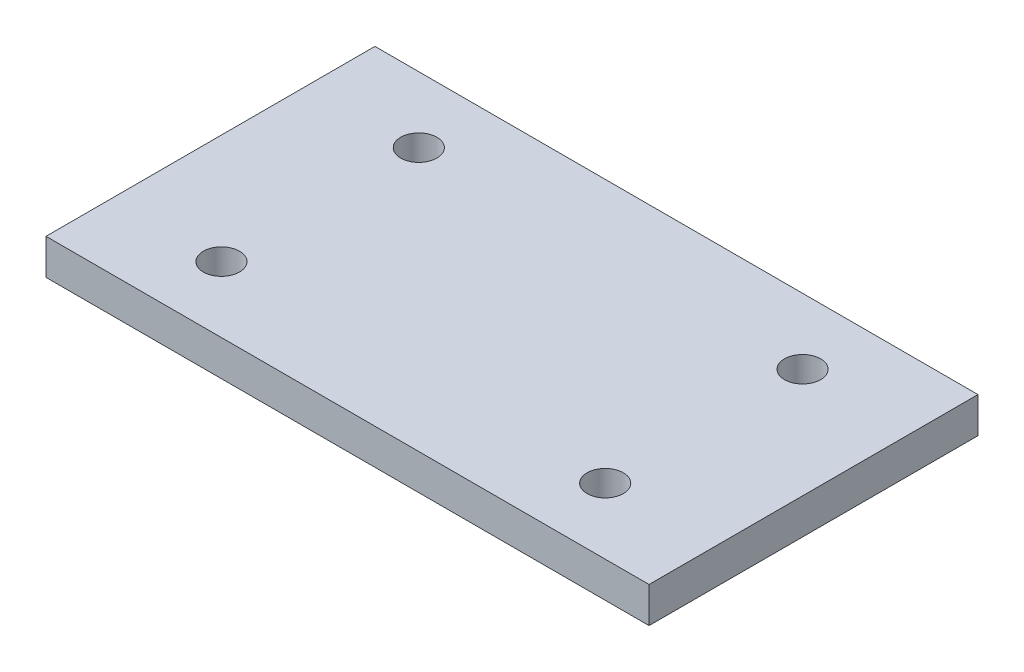
SolidWorks part; units mm, degrees
ref_plane "Front Plane" through (0, 0, 0) normal (0, 0, 1) x (1, 0, 0)
ref_plane "Top Plane" through (0, 0, 0) normal (0, 1, 0) x (1, 0, 0)
ref_plane "Right Plane" through (0, 0, 0) normal (1, 0, 0) x (0, 0, -1)
sketch "Sketch1" plane through (0, 0, 0) normal (0, 1, 0) x (1, 0, 0)
  line L1 (-27.5, -15) -> (27.5, -15)
  line L2 (-27.5, -15) -> (-27.5, 15)
  line L3 (-27.5, 15) -> (27.5, 15)
  line L4 (27.5, -15) -> (27.5, 15)
  line L5 (-27.5, -15) -> (27.5, 15) construction
  line L6 (-27.5, 15) -> (27.5, -15) construction
  line L7 (-17.5, -9) -> (17.5, -9) construction
  line L8 (-17.5, -9) -> (-17.5, 9) construction
  line L9 (-17.5, 9) -> (17.5, 9) construction
  line L10 (17.5, -9) -> (17.5, 9) construction
  line L11 (-17.5, -9) -> (17.5, 9) construction
  line L12 (-17.5, 9) -> (17.5, -9) construction
  circle A0 centre (-17.5, 9) radius 1.65
  circle A1 centre (17.5, 9) radius 1.65
  circle A2 centre (17.5, -9) radius 1.65
  circle A3 centre (-17.5, -9) radius 1.65
  point P1 (0, 0)
  point P6 (0, 0)
  dimension "D5" = 3.3
  dimension "D1" = 55
  dimension "D2" = 30
  dimension "D3" = 35
  dimension "D4" = 18
extrude "Boss-Extrude1" add sketch "Sketch1" along normal blind 3.25
